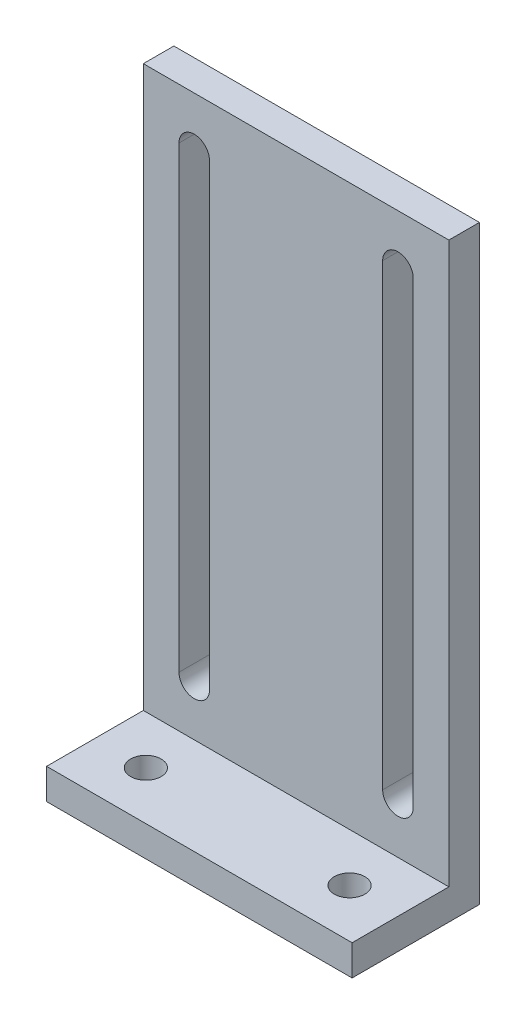
SolidWorks part; units mm, degrees
ref_plane "Front Plane" through (0, 0, 0) normal (0, 0, 1) x (1, 0, 0)
ref_plane "Top Plane" through (0, 0, 0) normal (0, 1, 0) x (1, 0, 0)
ref_plane "Right Plane" through (0, 0, 0) normal (1, 0, 0) x (0, 0, -1)
sketch "Sketch1" plane through (0, 0, 0) normal (0, 1, 0) x (1, 0, 0)
  line L1 (15, 6.25) -> (-15, 6.25)
  line L2 (15, 6.25) -> (15, -6.25)
  line L3 (15, -6.25) -> (-15, -6.25)
  line L4 (-15, 6.25) -> (-15, -6.25)
  line L5 (15, 6.25) -> (-15, -6.25) construction
  line L6 (15, -6.25) -> (-15, 6.25) construction
  point P0 (0, 0)
  dimension "D1" = 30
  dimension "D2" = 12.5
extrude "Boss-Extrude1" add sketch "Sketch1" along normal blind 3 contours L3 L4 L1 L2
sketch "Sketch2" plane through (0, 3, 0) normal (0, 1, 0) x (1, 0, 0)
  line L0 (15, 6.25) -> (15, -6.25) construction
  line L1 (-15, 6.25) -> (15, 6.25)
  line L2 (-15, 6.25) -> (-15, 3.25)
  line L3 (-15, 3.25) -> (15, 3.25)
  line L4 (15, 6.25) -> (15, 3.25)
  dimension "D1" = 3
extrude "Boss-Extrude2" add sketch "Sketch2" along normal blind 55
sketch "Sketch3" plane through (0, 0, -3.25) normal (0, 0, 1) x (1, 0, 0)
  line L0 (0, 58) -> (0, 3) construction
  line L5 (-15, 58) -> (15, 58) construction
  line L6 (15, 3) -> (-15, 3) construction
  line L7 (0, 30.5) -> (-15, 30.5) construction
  line L11 (10, 53) -> (10, 8) construction
  line L16 (-10, 53) -> (-10, 8) construction
  line L17 (-8.5, 53) -> (-8.5, 8)
  line L18 (-11.5, 53) -> (-11.5, 8)
  line L19 (8.5, 53) -> (8.5, 8)
  line L20 (11.5, 53) -> (11.5, 8)
  line L21 (-10, 53) -> (10, 53) construction
  line L22 (-15, 58) -> (-15, 3) construction
  arc A0 (-8.5, 53) -> (-11.5, 53) centre (-10, 53) ccw
  arc A1 (-11.5, 8) -> (-8.5, 8) centre (-10, 8) ccw
  arc A2 (8.5, 53) -> (11.5, 53) centre (10, 53) cw
  arc A3 (11.5, 8) -> (8.5, 8) centre (10, 8) cw
  point P13 (10, 30.5)
  point P18 (-10, 30.5)
  point P34 (5.85, 8)
  point P37 (9.15, 8)
  point P40 (9.15, 48)
  point P43 (5.85, 48)
  dimension "D3" = 20
  dimension "D1" = 45
  dimension "D2" = 1.5
extrude "Cut-Extrude1" cut sketch "Sketch3" against normal through all
sketch "Sketch4" plane through (0, 3, 0) normal (0, 1, 0) x (1, 0, 0)
  line L0 (-15, -1.5) -> (15, -1.5) construction
  line L7 (-10, 0.875) -> (-15, 0.875) construction
  line L8 (-15, 3.25) -> (-15, -6.25) construction
  line L12 (15, 3.25) -> (15, -6.25) construction
  line L14 (0, -3.875) -> (-7.5, -3.875) construction
  line L15 (15, -6.25) -> (-15, -6.25) construction
  line L22 (0, -1.5) -> (0, -6.25) construction
  line L25 (-15, -6.25) -> (-2.5, -6.25) construction
  circle A4 centre (-10, -1.5) radius 1.5
  circle A5 centre (10, -1.5) radius 1.5
  point P0 (7.2282, -1.416)
  dimension "D1" = 7.5
  dimension "D2" = 12.5
  dimension "D3" = 5
extrude "Cut-Extrude2" cut sketch "Sketch4" against normal through all
